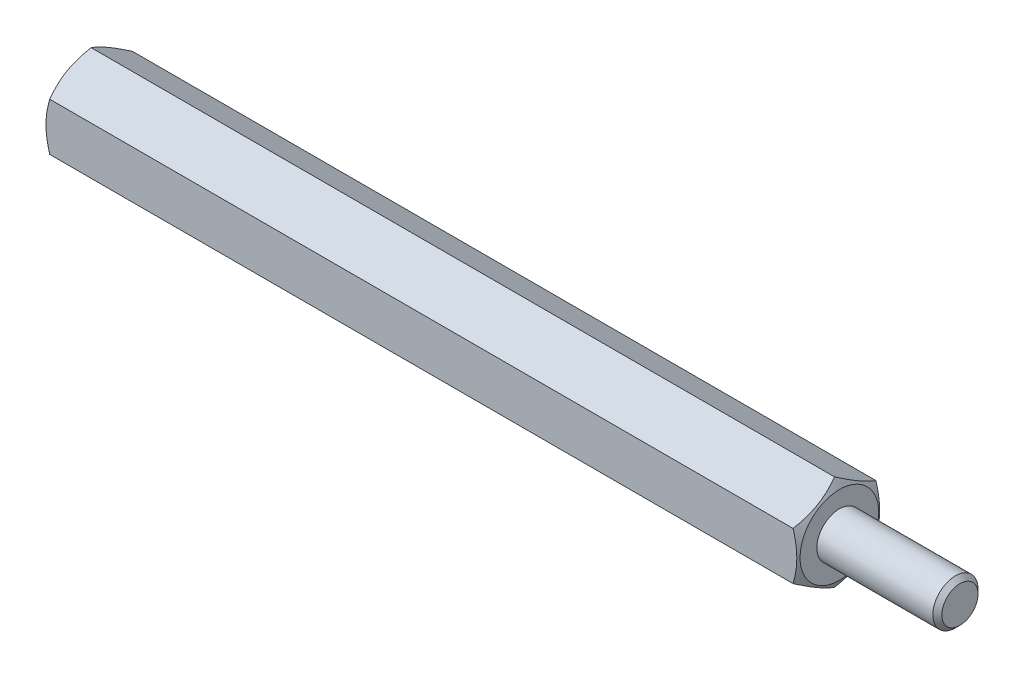
SolidWorks part; units mm, degrees
material "Brass"
ref_plane "Front Plane" through (0, 0, 0) normal (0, 0, 1) x (1, 0, 0)
ref_plane "Top Plane" through (0, 0, 0) normal (0, 1, 0) x (1, 0, 0)
ref_plane "Right Plane" through (0, 0, 0) normal (1, 0, 0) x (0, 0, -1)
sketch "Sketch1" plane through (0, 0, 0) normal (1, 0, 0) x (0, 0, -1)
  line L1 (0, 3.1754) -> (-2.75, 1.5877)
  line L2 (-2.75, 1.5877) -> (-2.75, -1.5877)
  line L3 (-2.75, -1.5877) -> (0, -3.1754)
  line L4 (0, -3.1754) -> (2.75, -1.5877)
  line L5 (2.75, -1.5877) -> (2.75, 1.5877)
  line L6 (2.75, 1.5877) -> (0, 3.1754)
  circle A0 centre (0, 0) radius 2.75 construction
extrude "Boss-Extrude1" add sketch "Sketch1" along normal blind 50
sketch "Sketch2" plane through (50, 0, 0) normal (1, 0, 0) x (0, 0, -1)
  circle A0 centre (0, 0) radius 1.5
extrude "Boss-Extrude2" add sketch "Sketch2" along normal blind 8
sketch "Sketch3" plane through (0, 0, 0) normal (-1, 0, 0) x (0, 0, 1)
  circle A0 centre (0, 0) radius 1.5
extrude "Cut-Extrude1" cut sketch "Sketch3" against normal blind 10
sketch "Sketch4" plane through (0, 0, 0) normal (0, 1, 0) x (1, 0, 0)
  line L0 (0, 0) -> (0, 2.6125)
  line L1 (0, 2.6125) -> (4.3921, 10.2198)
  line L2 (0, 2.6125) -> (0, 10.2198)
  line L3 (0, 10.2198) -> (4.3921, 10.2198)
  line L4 (0, 0) -> (-8.2035, 0) construction
  line L5 (50, 0) -> (50, 2.6125)
  line L6 (50, 2.6125) -> (45.6079, 10.2198)
  line L7 (50, 2.6125) -> (50, 10.2198)
  line L8 (50, 10.2198) -> (45.6079, 10.2198)
  line L9 (0, 0) -> (50, 0)
  dimension "D1" = 50
revolve "Cut-Revolve1" cut sketch "Sketch4" angle 360 about L4
chamfer "Chamfer1" distance 0.3 angle 45 1 edges at (58, 0, -1.5)
